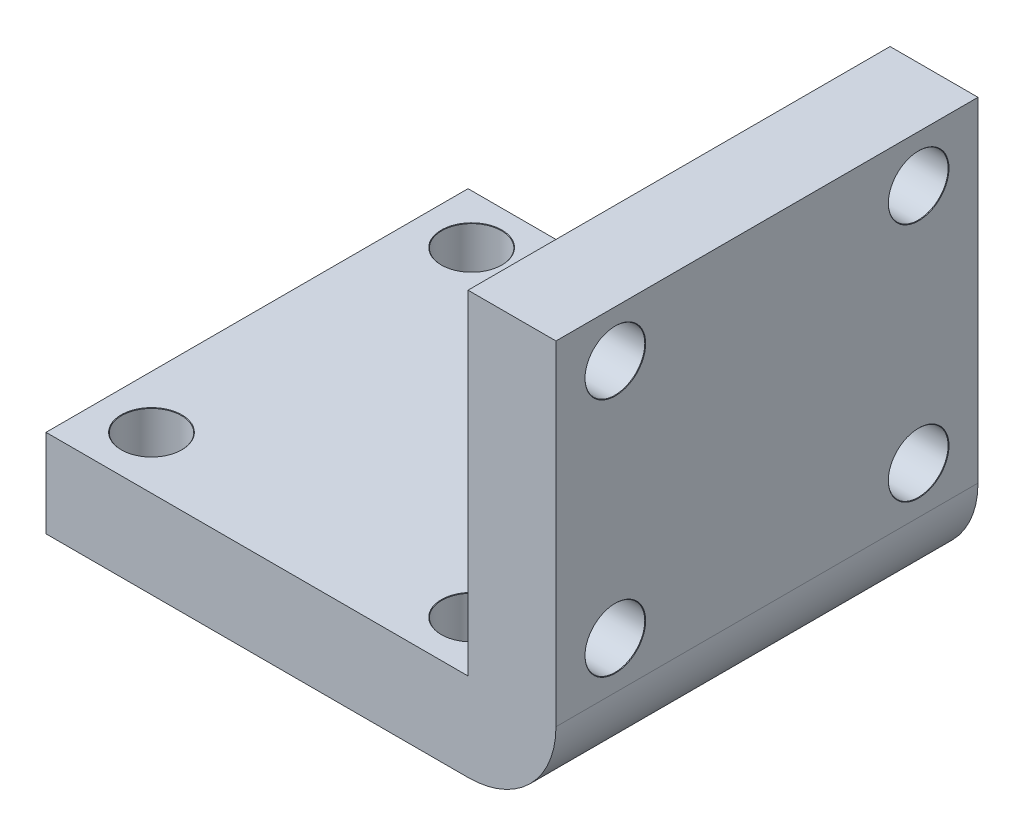
SolidWorks part; units mm, degrees
ref_plane "Front Plane" through (0, 0, 0) normal (0, 0, 1) x (1, 0, 0)
ref_plane "Top Plane" through (0, 0, 0) normal (0, 1, 0) x (1, 0, 0)
ref_plane "Right Plane" through (0, 0, 0) normal (1, 0, 0) x (0, 0, -1)
sketch "Sketch1" plane through (0, 0, 0) normal (0, 1, 0) x (1, 0, 0)
  line L1 (12, -12) -> (-12, -12)
  line L2 (12, -12) -> (12, 12)
  line L3 (12, 12) -> (-12, 12)
  line L4 (-12, -12) -> (-12, 12)
  line L5 (12, -12) -> (-12, 12) construction
  line L6 (12, 12) -> (-12, -12) construction
  point P0 (0, 0)
  dimension "D1" = 24
  dimension "D2" = 24
extrude "Boss-Extrude1" add sketch "Sketch1" along normal blind 5
sketch "Sketch2" plane through (0, 0, 0) normal (1, 0, 0) x (0, 0, -1)
  line L0 (-12, 0) -> (12, 0) construction
  line L1 (12, 0) -> (-12, 0)
  line L2 (12, 0) -> (12, 24)
  line L3 (12, 24) -> (-12, 24)
  line L4 (-12, 0) -> (-12, 24)
  line L5 (12, 0) -> (-12, 24) construction
  line L6 (12, 24) -> (-12, 0) construction
  point P0 (0, 12)
  dimension "D1" = 24
  dimension "D2" = 24
extrude "Boss-Extrude2" add sketch "Sketch2" along normal blind 5 from surface at 12 starting at face at (12, 2.5, 0)
fillet "Fillet3" radius 5 1 edges at (17, 0, 0)
sketch "Sketch4" plane through (17, 0, 0) normal (1, 0, 0) x (0, 0, -1)
  line L6 (12, 24) -> (-12, 5) construction
  line L10 (-12, 24) -> (12, 5) construction
  circle A0 centre (0, 14.5) radius 5
  point P0 (-8.6245, 21.3277)
  point P73 (8.6245, 21.3277)
  point P75 (8.6245, 7.6723)
  point P77 (-8.6245, 7.6723)
  dimension "D1" = 10
  dimension "D2" = 11
hole_wizard "M3 Clearance Hole1" positions "Sketch4" profile "Sketch5" hole size "M3" standard "ISO" end condition through all
sketch "Sketch5" plane through (17, 21.3277, 8.6245) normal (0, 1, 0) x (0, 0, -1)
  line L0 (0, 0) -> (0, 29)
  line L1 (0, 29) -> (1.7, 29)
  line L2 (1.7, 29) -> (1.7, 0.025)
  line L3 (1.7, 0.025) -> (1.725, 0)
  line L5 (1.725, 0) -> (0, 0)
  line L6 (-1.7, 0.025) -> (-1.725, 0) construction
  line L11 (0, -6.35) -> (0, 107.95) construction
  dimension "Thru Hole Dia." = 3.4
  dimension "Thru Hole Depth" = 29
  dimension "Near C'Sink Dia." = 3.45
  dimension "Near C'Sink Angle" = 90
sketch "Sketch8" plane through (0, 5, 0) normal (0, 1, 0) x (1, 0, 0)
  circle A0 centre (0, 0) radius 7.5 construction
  dimension "D1" = 15
hole_wizard "M3 Clearance Hole2" positions "Sketch6" profile "Sketch7" hole size "M3" standard "ISO" end condition through all
sketch "Sketch6" plane through (0, 5, 0) normal (0, 1, 0) x (1, 0, 0)
  line L0 (0, 0) -> (0, -12) construction
  line L2 (-12, -12) -> (12, -12) construction
  line L3 (0, 0) -> (-12, 0) construction
  line L4 (-12, 12) -> (-12, -12) construction
  line L7 (12, 12) -> (-12, -12) construction
  point P0 (-9, -9)
  point P35 (-9, 9.2037)
  point P37 (9.2037, 9.2037)
  point P39 (9.2037, -9)
  dimension "D1" = 9
sketch "Sketch7" plane through (-9, 5, 9) normal (1, 0, 0) x (0, 0, 1)
  line L0 (0, 0) -> (0, 5)
  line L1 (0, 5) -> (1.7, 5)
  line L2 (1.7, 5) -> (1.7, 0.025)
  line L3 (1.7, 0.025) -> (1.725, 0)
  line L5 (1.725, 0) -> (0, 0)
  line L6 (-1.7, 0.025) -> (-1.725, 0) construction
  line L11 (0, -6.35) -> (0, 107.95) construction
  dimension "Thru Hole Dia." = 3.4
  dimension "Thru Hole Depth" = 5
  dimension "Near C'Sink Dia." = 3.45
  dimension "Near C'Sink Angle" = 90
